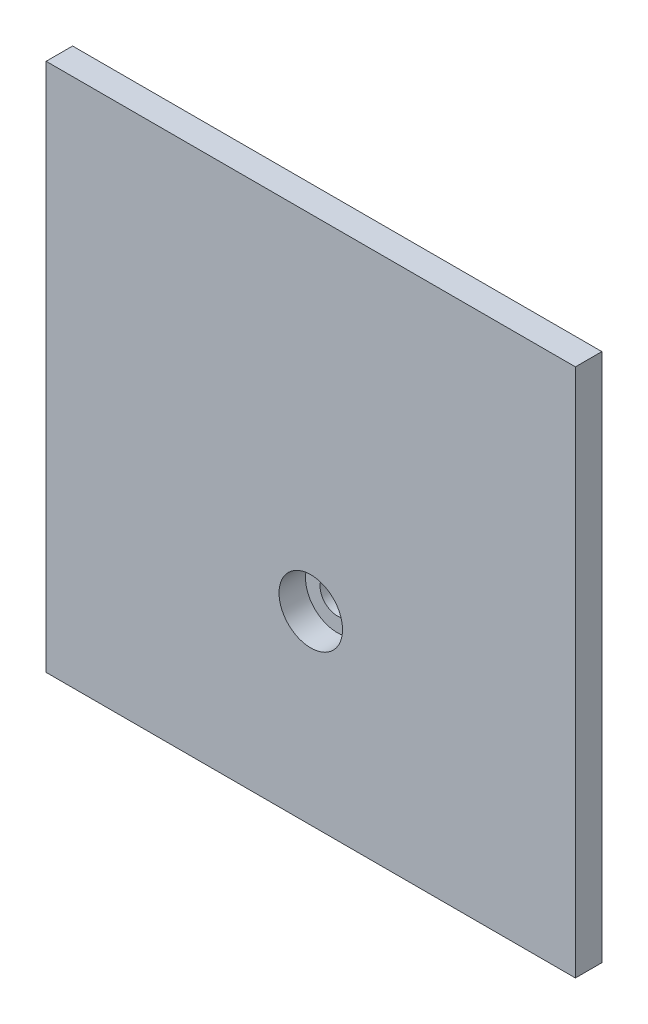
SolidWorks part; units mm, degrees
ref_plane "Plan de face" through (0, 0, 0) normal (0, 0, 1) x (1, 0, 0)
ref_plane "Plan de dessus" through (0, 0, 0) normal (0, 1, 0) x (1, 0, 0)
ref_plane "Plan de droite" through (0, 0, 0) normal (1, 0, 0) x (0, 0, -1)
sketch "Esquisse1" plane through (0, 0, 0) normal (0, 0, 1) x (1, 0, 0)
  line L1 (-50, 50) -> (50, 50)
  line L2 (-50, 50) -> (-50, -50)
  line L3 (-50, -50) -> (50, -50)
  line L4 (50, 50) -> (50, -50)
  line L5 (-50, 50) -> (50, -50) construction
  line L6 (-50, -50) -> (50, 50) construction
  point P0 (0, 0)
  dimension "D1" = 100
  dimension "D2" = 100
extrude "Boss.-Extru.1" add sketch "Esquisse1" along normal blind 5
sketch "Esquisse4" plane through (0, 0, 0) normal (0, 0, -1) x (-1, 0, 0)
  line L0 (-15, 45) -> (15, 45)
  line L1 (15, 45) -> (15, -15)
  line L2 (15, -15) -> (-15, -15) construction
  line L3 (-15, -15) -> (-15, 45)
  line L4 (-50, 50) -> (50, 50) construction
  line L5 (50, -50) -> (-50, -50) construction
  line L6 (-15, 0) -> (15, 0) construction
  line L7 (0, 45) -> (0, -15) construction
  line L8 (-50, -50) -> (-50, 50) construction
  arc A0 (-15, -15) -> (15, -15) centre (0, -15) ccw
  dimension "D4" = 15
  dimension "D1" = 5
  dimension "D2" = 35
  dimension "D3" = 15
  dimension "D5" = 50
extrude "Boss.-Extru.2" add sketch "Esquisse4" along normal blind 30
sketch "Esquisse5" plane through (15, 0, 0) normal (1, 0, 0) x (0, 0, -1)
  line L0 (0, 45) -> (30, 0)
  line L1 (30, 45) -> (30, -15) construction
  line L3 (30, 0) -> (0, 0) construction
  line L4 (0, 45) -> (0, -15) construction
  line L5 (30, -15) -> (0, -15) construction
  line L6 (30, 0) -> (30, 45)
  line L7 (30, 45) -> (0, 45)
  dimension "D1" = 15
extrude "Enlèv. mat.-Extru.1" cut sketch "Esquisse5" against normal blind 30
sketch "Esquisse6" plane through (0, 0, -30) normal (0, 0, -1) x (-1, 0, 0)
  line L0 (15, 0) -> (-15, 0) construction
  circle A0 centre (0, -15) radius 3.25
  dimension "D2" = 6.5
  dimension "D1" = 15
extrude "Enlèv. mat.-Extru.2" cut sketch "Esquisse6" against normal blind 35
sketch "Esquisse7" plane through (0, 0, 5) normal (0, 0, 1) x (1, 0, 0)
  circle A0 centre (0, -15) radius 6
  dimension "D1" = 12
extrude "Enlèv. mat.-Extru.3" cut sketch "Esquisse7" against normal blind 5
